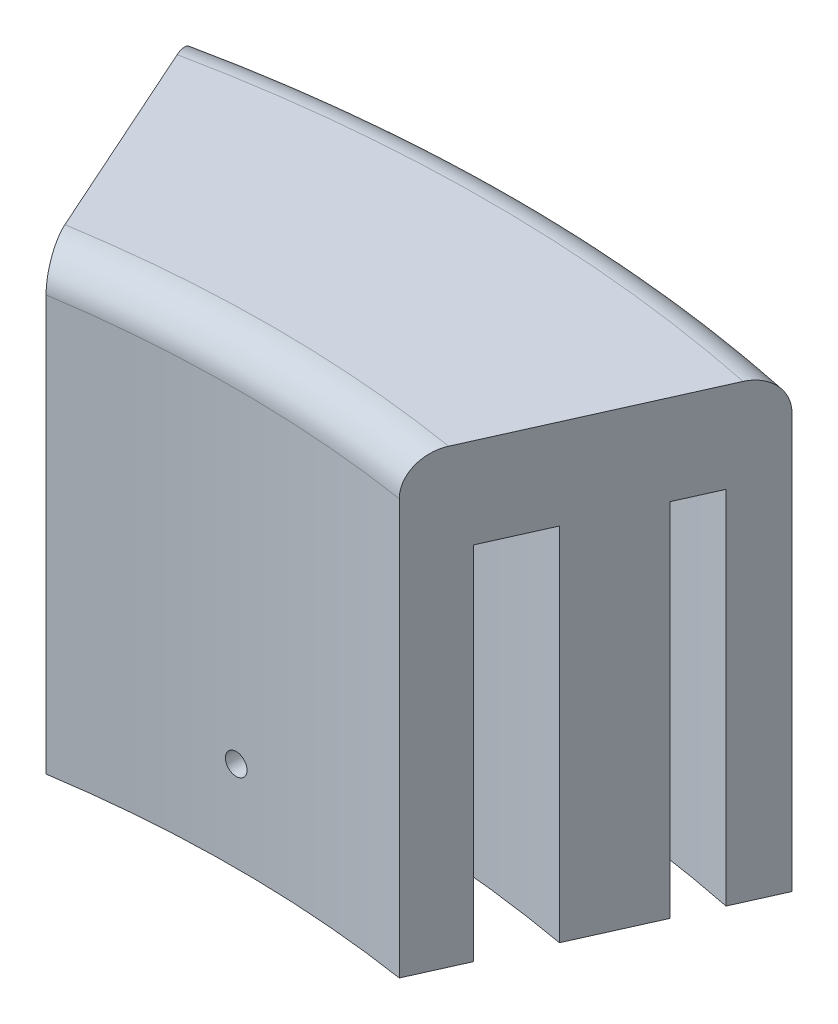
SolidWorks part; units mm, degrees
ref_plane "Front Plane" through (0, 0, 0) normal (0, 0, 1) x (1, 0, 0)
ref_plane "Top Plane" through (0, 0, 0) normal (0, 1, 0) x (1, 0, 0)
ref_plane "Right Plane" through (0, 0, 0) normal (1, 0, 0) x (0, 0, -1)
sketch "Sketch1" plane through (0, 0, 0) normal (0, 1, 0) x (1, 0, 0)
  line L0 (12.4292, 80.3241) -> (20.978, 99.4107)
  line L1 (-12.4292, 80.3241) -> (-20.978, 99.4107)
  line L2 (0, 0) -> (0, 101.6) construction
  arc A0 (-20.978, 99.4107) -> (20.978, 99.4107) centre (0, 0) cw
  arc A1 (-12.4292, 80.3241) -> (12.4292, 80.3241) centre (0, 0) cw
  dimension "D1" = 101.6
  dimension "D2" = 81.28
extrude "Boss-Extrude1" add sketch "Sketch1" along normal blind 31.75
sketch "Sketch3" plane through (0, 0, 0) normal (0, -1, 0) x (1, 0, 0)
  line L0 (-14.0413, -83.9235) -> (-15.916, -88.109)
  line L1 (15.916, -88.109) -> (14.0413, -83.9235)
  line L2 (12.4292, -80.3241) -> (20.978, -99.4107) construction
  line L3 (-20.978, -99.4107) -> (-12.4292, -80.3241) construction
  arc A0 (-15.916, -88.109) -> (15.916, -88.109) centre (0, 0) ccw
  arc A1 (-14.0413, -83.9235) -> (14.0413, -83.9235) centre (0, 0) ccw
  dimension "D1" = 89.535
  dimension "D2" = 85.09
extrude "Cut-Extrude1" cut sketch "Sketch3" against normal blind 25.4
fillet "Fillet1" radius 2.54 2 edges at (0, 31.75, -81.28) (0, 31.75, -101.6)
sketch "Sketch4" plane through (0, 0, 0) normal (0, -1, 0) x (1, 0, 0)
  line L0 (-25.7868, -94.7237) -> (-24.259, -92.109)
  line L1 (46.5277, -86.4449) -> (44.4484, -84.2431)
  arc A0 (-24.259, -92.109) -> (44.4484, -84.2431) centre (0, 0) ccw
  arc A1 (-25.7868, -94.7237) -> (46.5277, -86.4449) centre (0, 0) ccw
  dimension "D1" = 95.25
  dimension "D2" = 98.171
extrude "Cut-Extrude2" cut sketch "Sketch4" against normal blind 25.4
sketch "Sketch5" plane through (0, 0, 0) normal (0, 0, 1) x (1, 0, 0)
  line L0 (-12.4292, 0) -> (12.4292, 0) construction
  circle A0 centre (0, 6.35) radius 0.762
  point P4 (0, 0)
  dimension "D1" = 1.524
  dimension "D2" = 6.35
extrude "Cut-Extrude3" cut sketch "Sketch5" against normal blind 266.7
